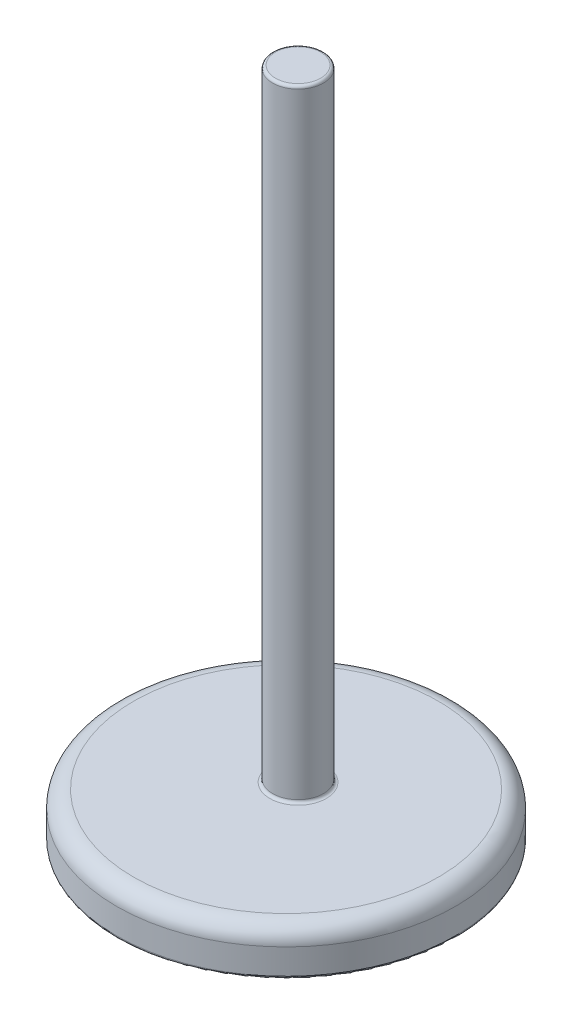
SolidWorks part; units mm, degrees
ref_plane "Front Plane" through (0, 0, 0) normal (0, 0, 1) x (1, 0, 0)
ref_plane "Top Plane" through (0, 0, 0) normal (0, 1, 0) x (1, 0, 0)
ref_plane "Right Plane" through (0, 0, 0) normal (1, 0, 0) x (0, 0, -1)
sketch "Sketch1" plane through (0, 0, 0) normal (0, 1, 0) x (1, 0, 0)
  circle A0 centre (0, 0) radius 60
  dimension "D1" = 120
extrude "Boss-Extrude1" add sketch "Sketch1" along normal blind 16
sketch "Sketch2" plane through (0, 16, 0) normal (0, 1, 0) x (1, 0, 0)
  circle A0 centre (0, 4.2533) radius 9
extrude "Boss-Extrude2" add sketch "Sketch2" along normal blind 220
cosmetic thread "Cosmetic Thread1" parameters "D2"=15.797
cosmetic thread "Cosmetic Thread2" parameters "D2"=6.619
fillet "Fillet1" radius 6 1 edges at (0, 16, 60)
fillet "Fillet2" radius 1 3 edges at (0, 0, 60) (0, 16, 4.7467) (0, 236, 4.7467)
